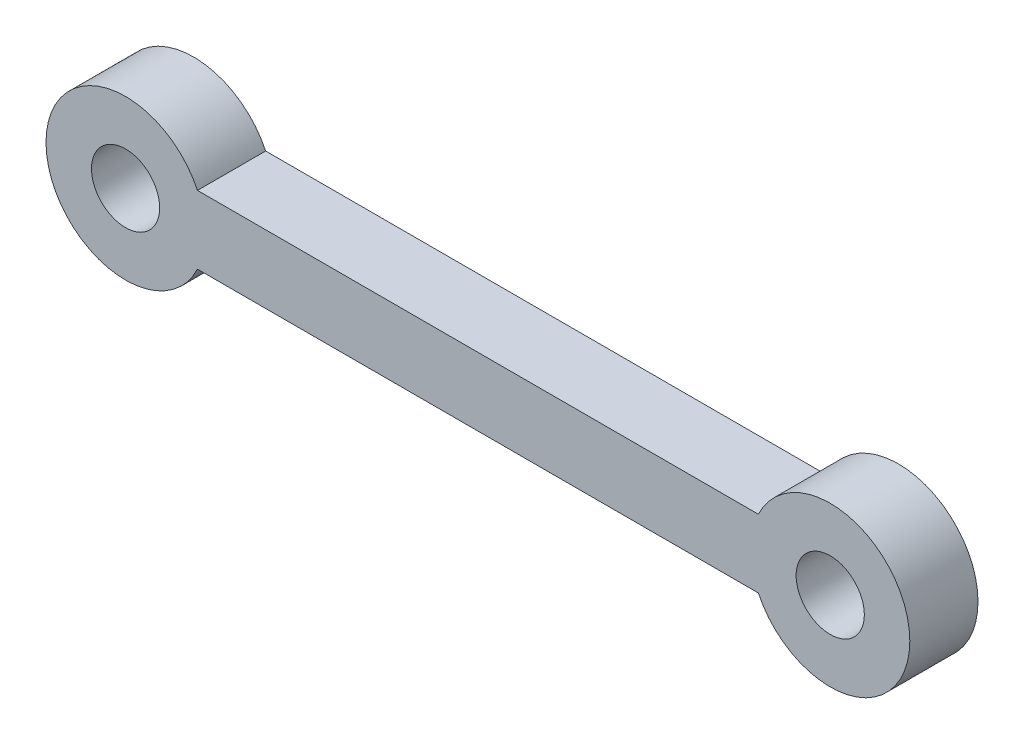
SolidWorks part; units mm, degrees
ref_plane "前视基准面" through (0, 0, 0) normal (0, 0, 1) x (1, 0, 0)
ref_plane "上视基准面" through (0, 0, 0) normal (0, 1, 0) x (1, 0, 0)
ref_plane "右视基准面" through (0, 0, 0) normal (1, 0, 0) x (0, 0, -1)
other "Configuration Table"
sketch "草图1" plane through (0, 0, 0) normal (0, 0, 1) x (1, 0, 0)
  line L0 (0, 0) -> (31, 0) construction
  line L1 (0, 3.5) -> (31, 3.5) construction
  line L2 (0, -3.5) -> (31, -3.5) construction
  line L3 (15.5, 0) -> (15.5, -3.5) construction
  line L5 (3.1623, -1.5) -> (27.8377, -1.5)
  line L6 (3.1623, -1.5) -> (3.1623, 1.5)
  line L7 (3.1623, 1.5) -> (27.8377, 1.5)
  line L8 (27.8377, -1.5) -> (27.8377, 1.5)
  line L9 (3.1623, -1.5) -> (27.8377, 1.5) construction
  line L10 (3.1623, 1.5) -> (27.8377, -1.5) construction
  arc A0 (0, 3.5) -> (0, -3.5) centre (0, 0) ccw construction
  arc A1 (31, -3.5) -> (31, 3.5) centre (31, 0) ccw construction
  circle A2 centre (0, 0) radius 3.5
  circle A3 centre (0, 0) radius 1.5
  circle A4 centre (31, 0) radius 3.5
  circle A5 centre (31, 0) radius 1.5
  point P3 (15.5, 0)
  dimension "D2" = 3.5
  dimension "D3" = 3
  dimension "D1" = 31
  dimension "D4" = 3
extrude "凸台-拉伸1" add sketch "草图1" along normal blind 3 contours L6 A2 A3 | L5 A4 L7 A2 | A4 L8 A5 | L6 A2 | A4 L8
